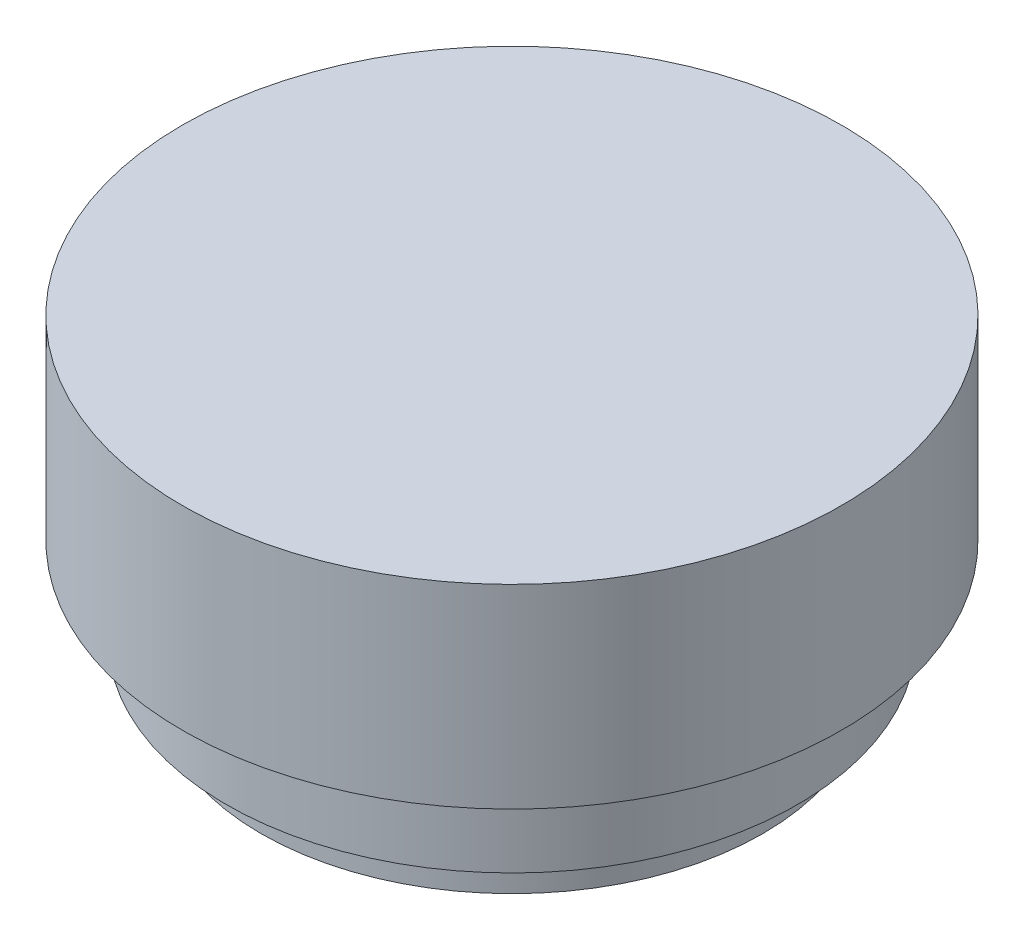
SolidWorks part; units mm, degrees
ref_plane "Front Plane" through (0, 0, 0) normal (0, 0, 1) x (1, 0, 0)
ref_plane "Top Plane" through (0, 0, 0) normal (0, 1, 0) x (1, 0, 0)
ref_plane "Right Plane" through (0, 0, 0) normal (1, 0, 0) x (0, 0, -1)
sketch "Sketch1" plane through (0, 0, 0) normal (0, 0, 1) x (1, 0, 0)
  line L0 (-29, 6.6) -> (-29, 11.5)
  line L1 (-29, 11.5) -> (-33, 11.5)
  line L2 (-33, 11.5) -> (-33, 21.5)
  line L3 (-33, 21.5) -> (-38.1, 21.5)
  line L4 (-38.1, 21.5) -> (-38.1, 44)
  line L5 (-38.1, 44) -> (0, 44)
  line L6 (0, 44) -> (0, 6.6)
  line L7 (0, 6.6) -> (-29, 6.6)
  point P5 (-29, 9.05)
  dimension "D1" = 6.6
  dimension "D2" = 11.5
  dimension "D3" = 44
  dimension "D4" = 10
  dimension "D5" = 29
  dimension "D6" = 33
  dimension "D7" = 38.1
revolve "Revolve1" add sketch "Sketch1" angle 360 about L6
